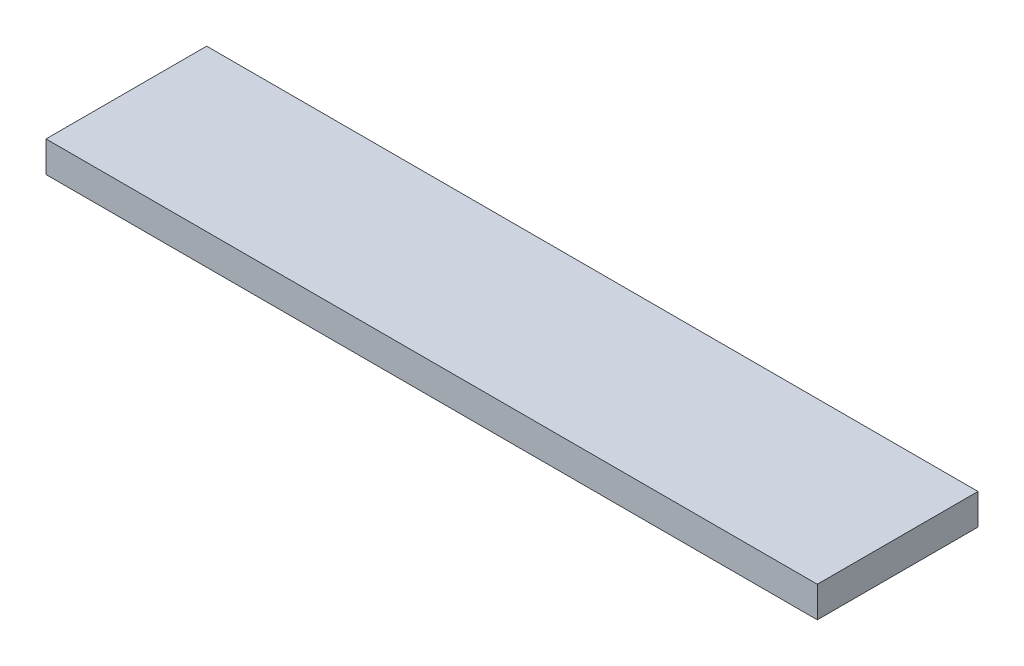
SolidWorks part; units mm, degrees
ref_plane "Front Plane" through (0, 0, 0) normal (0, 0, 1) x (1, 0, 0)
ref_plane "Top Plane" through (0, 0, 0) normal (0, 1, 0) x (1, 0, 0)
ref_plane "Right Plane" through (0, 0, 0) normal (1, 0, 0) x (0, 0, -1)
sketch "Sketch1" plane through (0, 0, 0) normal (0, 1, 0) x (1, 0, 0)
  line L1 (-150, 31.25) -> (150, 31.25)
  line L2 (-150, 31.25) -> (-150, -31.25)
  line L3 (-150, -31.25) -> (150, -31.25)
  line L4 (150, 31.25) -> (150, -31.25)
  line L5 (-150, 31.25) -> (150, -31.25) construction
  line L6 (-150, -31.25) -> (150, 31.25) construction
  point P0 (0, 0)
  dimension "D1" = 62.5
  dimension "D2" = 300
extrude "Boss-Extrude1" add sketch "Sketch1" along normal blind 12
